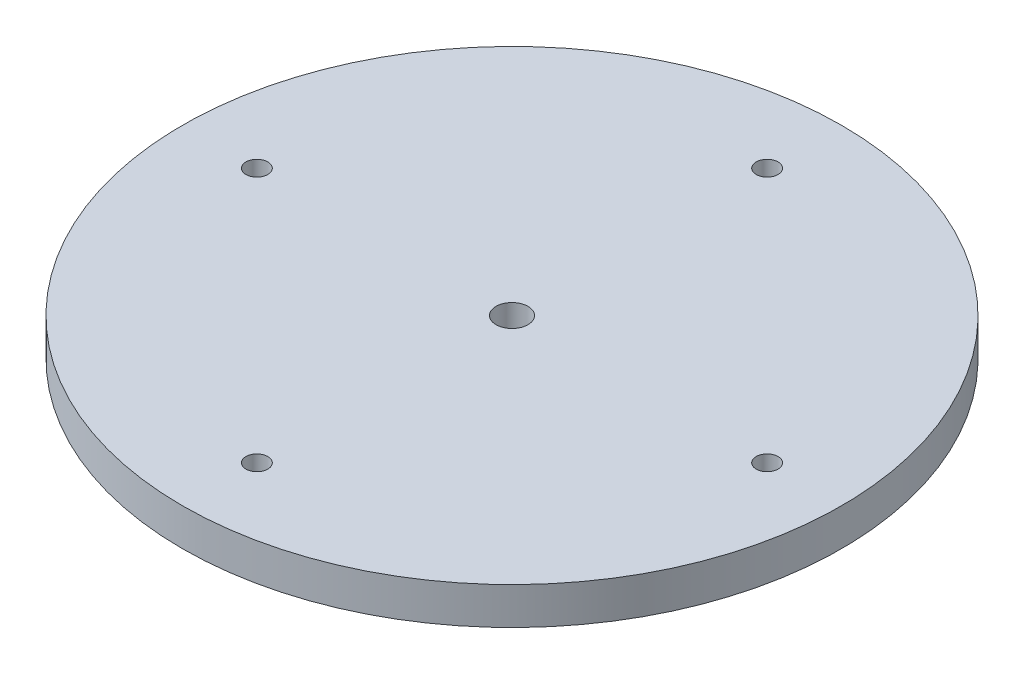
SolidWorks part; units mm, degrees
material "AISI 316 Stainless Steel Sheet (SS)"
ref_plane "Front Plane" through (0, 0, 0) normal (0, 0, 1) x (1, 0, 0)
ref_plane "Top Plane" through (0, 0, 0) normal (0, 1, 0) x (1, 0, 0)
ref_plane "Right Plane" through (0, 0, 0) normal (1, 0, 0) x (0, 0, -1)
sketch "Sketch1" plane through (0, 0, 0) normal (0, 1, 0) x (1, 0, 0)
  circle A0 centre (0, 0) radius 98.425
  circle A1 centre (0, 0) radius 4.7625
  dimension "D1" = 9.525
  dimension "D2" = 196.85
extrude "Boss-Extrude1" add sketch "Sketch1" along normal blind 5.5562 and the other way blind 5.5562
hole_wizard "1/4 Clearance Hole1" positions "3DSketch1" profile "Sketch2" hole size "1/4" standard "ANSI Inch"
sketch3d "3DSketch1"
  line L0 (0, 0, 0) -> (0, 0, 76.2) construction
  point P0 (0, 5.5562, 76.2)
  point P15 (0, 0, 0)
  point P16 (0, 0, 45.1549)
sketch "Sketch2" plane through (0, 5.5562, 76.2) normal (1, 0, 0) x (0, 0, 1)
  line L0 (0, 0) -> (0, 14.6611)
  line L1 (0, 14.6611) -> (3.2639, 12.7)
  line L2 (3.2639, 12.7) -> (3.2639, 0)
  line L5 (3.2639, 0) -> (0, 0)
  line L10 (0, 14.6611) -> (-3.2639, 12.7) construction
  line L11 (0, -6.35) -> (0, 107.95) construction
  dimension "Hole Dia." = 6.5278
  dimension "Hole Depth" = 12.7
  dimension "Drill Angle" = 118
pattern_circular "CirPattern1" count 4 over 360 about axis through (0, 0, 0) along (0, 1, 0) of "1/4 Clearance Hole1"
